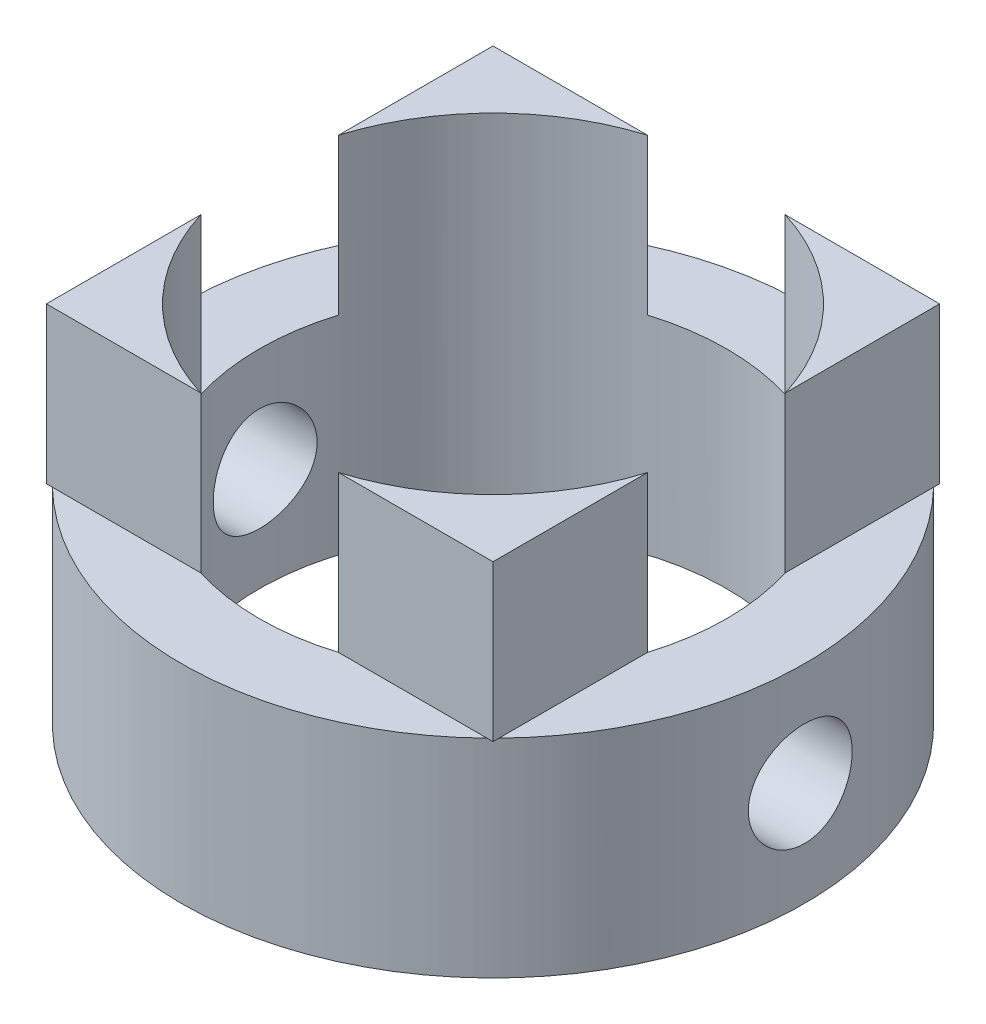
SolidWorks part; units mm, degrees
ref_plane "Front Plane" through (0, 0, 0) normal (0, 0, 1) x (1, 0, 0)
ref_plane "Top Plane" through (0, 0, 0) normal (0, 1, 0) x (1, 0, 0)
ref_plane "Right Plane" through (0, 0, 0) normal (1, 0, 0) x (0, 0, -1)
sketch "Sketch1" plane through (0, 0, 0) normal (0, 1, 0) x (1, 0, 0)
  circle A0 centre (0, 0) radius 6
  circle A1 centre (0, 0) radius 4.5
extrude "Boss-Extrude5" add sketch "Sketch1" along normal blind 4
sketch "Sketch3" plane through (0, 4, 0) normal (0, 1, 0) x (1, 0, 0)
  line L0 (1.3266, 4.3) -> (4.3, 4.3)
  line L1 (-4.3, -4.3) -> (-1.3266, -4.3)
  line L2 (-4.3, -4.3) -> (-4.3, -1.3266)
  line L3 (-4.3, 4.3) -> (-1.3266, 4.3)
  line L4 (4.3, -4.3) -> (4.3, -1.3266)
  line L5 (-4.3, -4.3) -> (4.3, 4.3) construction
  line L6 (-4.3, 4.3) -> (4.3, -4.3) construction
  line L7 (-4.3, 1.3266) -> (-4.3, 4.3)
  line L8 (1.3266, -4.3) -> (4.3, -4.3)
  line L9 (4.3, 1.3266) -> (4.3, 4.3)
  arc A0 (-1.3266, 4.3) -> (-4.3, 1.3266) centre (0, 0) ccw
  arc A1 (-4.3, -1.3266) -> (-1.3266, -4.3) centre (0, 0) ccw
  arc A2 (1.3266, -4.3) -> (4.3, -1.3266) centre (0, 0) ccw
  arc A3 (4.3, 1.3266) -> (1.3266, 4.3) centre (0, 0) ccw
  point P0 (0, 0)
  dimension "D1" = 8.6
  dimension "D2" = 8.6
extrude "Boss-Extrude6" add sketch "Sketch3" along normal blind 3
sketch "Sketch4" plane through (0, 0, 0) normal (1, 0, 0) x (0, 0, -1)
  line L0 (0, 0) -> (0, 4) construction
  line L1 (4.1845, 4) -> (-4.1845, 4) construction
  circle A0 centre (0, 2) radius 1
extrude "Cut-Extrude1" cut sketch "Sketch4" against normal through all both and the other way through all
